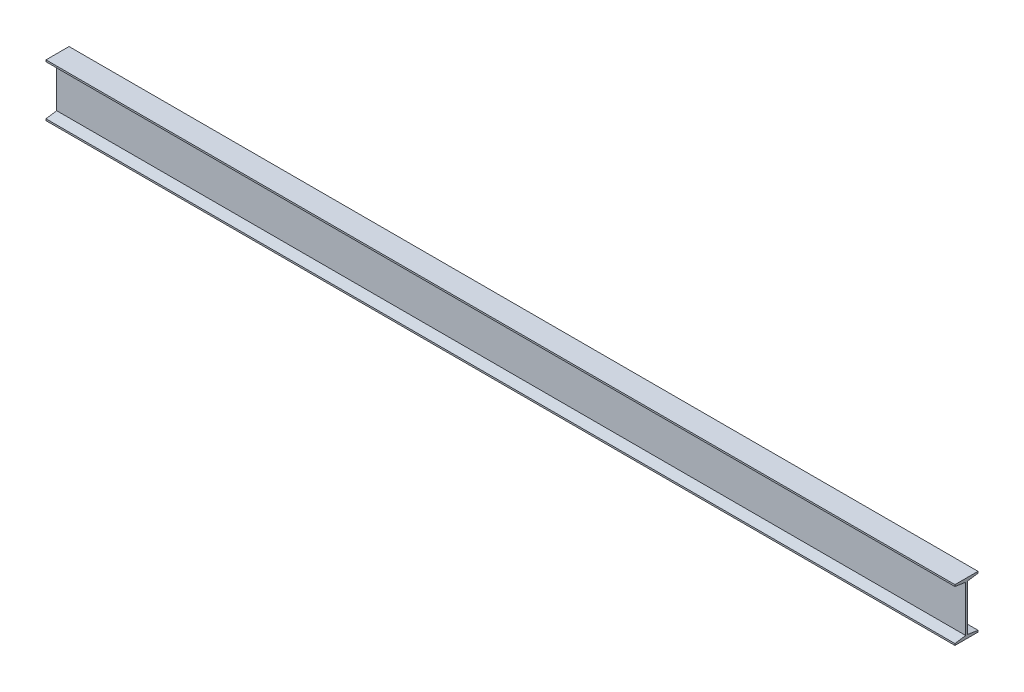
SolidWorks part; units mm, degrees
material "ASTM A36 Steel"
ref_plane "Front Plane" through (0, 0, 0) normal (0, 0, 1) x (1, 0, 0)
ref_plane "Top Plane" through (0, 0, 0) normal (0, 1, 0) x (1, 0, 0)
ref_plane "Right Plane" through (0, 0, 0) normal (1, 0, 0) x (0, 0, -1)
sketch "Sketch1" plane through (0, 0, 0) normal (1, 0, 0) x (0, 0, -1)
  line L12 (0, 0) -> (0, 6.35)
  line L13 (0, 6.35) -> (41.275, 12.7)
  line L14 (41.275, 12.7) -> (41.275, 190.5)
  line L16 (0, 203.2) -> (88.9, 203.2)
  line L18 (88.9, 0) -> (0, 0)
  line L19 (0, 203.2) -> (0, 196.85)
  line L20 (0, 196.85) -> (41.275, 190.5)
  line L21 (88.9, 196.85) -> (47.625, 190.5)
  line L22 (88.9, 203.2) -> (88.9, 196.85)
  line L23 (47.625, 12.7) -> (47.625, 190.5)
  line L24 (88.9, 6.35) -> (47.625, 12.7)
  line L25 (88.9, 0) -> (88.9, 6.35)
  dimension "D1" = 6.35
  dimension "D2" = 12.7
  dimension "D3" = 12.7
  dimension "D4" = 6.35
  dimension "D5" = 203.2
  dimension "D6" = 6.35
  dimension "D7" = 41.275
  dimension "D8" = 41.275
  dimension "D9" = 12.7
  dimension "D10" = 6.35
  dimension "D11" = 12.7
  dimension "D12" = 6.35
  dimension "D13" = 41.275
extrude "Boss-Extrude1" add sketch "Sketch1" along normal blind 3505.2 contours L16 L22 L21 L23 L24 L25 L18 L12 L13 L14 L20 L19
